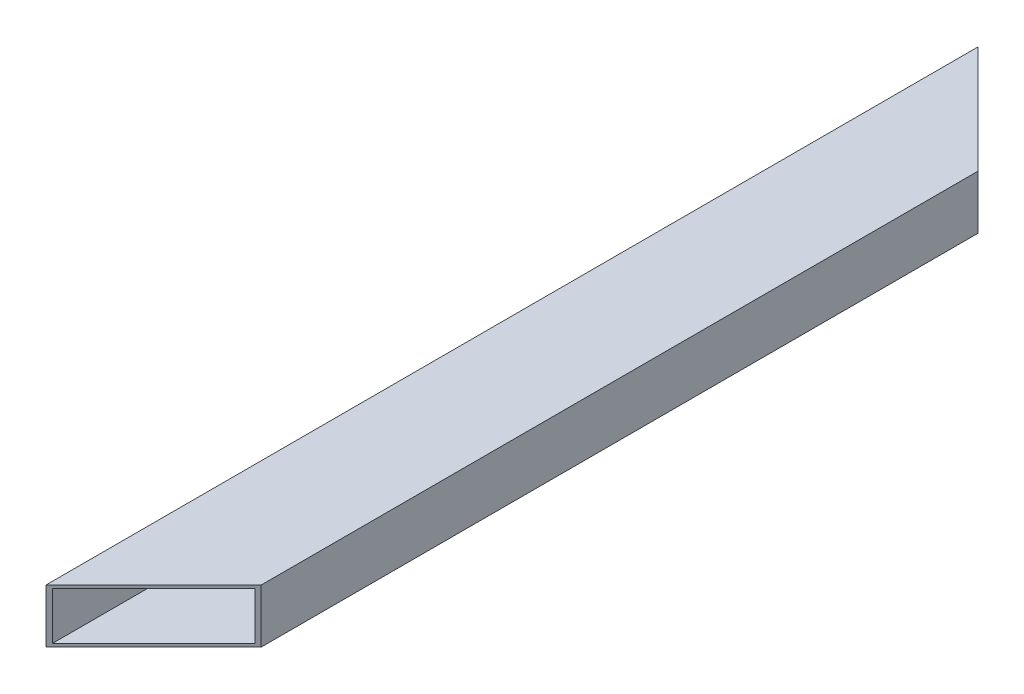
SolidWorks part; units mm, degrees
material "AISI 1015 Acero estirado en frío (SS)"
ref_plane "Alzado" through (0, 0, 0) normal (0, 0, 1) x (1, 0, 0)
ref_plane "Planta" through (0, 0, 0) normal (0, 1, 0) x (1, 0, 0)
ref_plane "Vista lateral" through (0, 0, 0) normal (1, 0, 0) x (0, 0, -1)
sketch "Croquis1" plane through (0, 0, 0) normal (0, 0, 1) x (1, 0, 0)
  line L0 (-23.9, -11.2) -> (-23.9, 11.2)
  line L1 (-25.4, -12.7) -> (25.4, -12.7)
  line L2 (-25.4, -12.7) -> (-25.4, 12.7)
  line L3 (-25.4, 12.7) -> (25.4, 12.7)
  line L4 (25.4, -12.7) -> (25.4, 12.7)
  line L5 (-25.4, -12.7) -> (25.4, 12.7) construction
  line L6 (-25.4, 12.7) -> (25.4, -12.7) construction
  line L7 (-23.9, 11.2) -> (23.9, 11.2)
  line L8 (23.9, -11.2) -> (23.9, 11.2)
  line L9 (-23.9, -11.2) -> (23.9, -11.2)
  point P0 (0, 0)
  dimension "D1" = 25.4
  dimension "D2" = 50.8
  dimension "D3" = 1.5
extrude "Saliente-Extruir1" add sketch "Croquis1" along normal blind 440
ref_plane "Plano1" through (0, 12.7, 0) normal (0, 1, 0) x (1, 0, 0)
sketch "Croquis2" plane through (0, 12.7, 0) normal (0, 1, 0) x (1, 0, 0)
  line L0 (25.4, -220) -> (-76.4991, -220) construction
  line L1 (25.4, -440) -> (25.4, 0) construction
  line L2 (-25.4, 0) -> (25.4, -50.8)
  line L3 (25.4, 0) -> (-25.4, 0) construction
  line L4 (25.4, -50.8) -> (25.4, 0)
  line L5 (25.4, 0) -> (-25.4, 0)
  line L6 (25.4, -389.2) -> (25.4, -440)
  line L7 (-25.4, -440) -> (25.4, -389.2)
  line L8 (25.4, -440) -> (-25.4, -440)
  dimension "D1" = 45
extrude "Cortar-Extruir1" cut sketch "Croquis2" against normal blind 26
